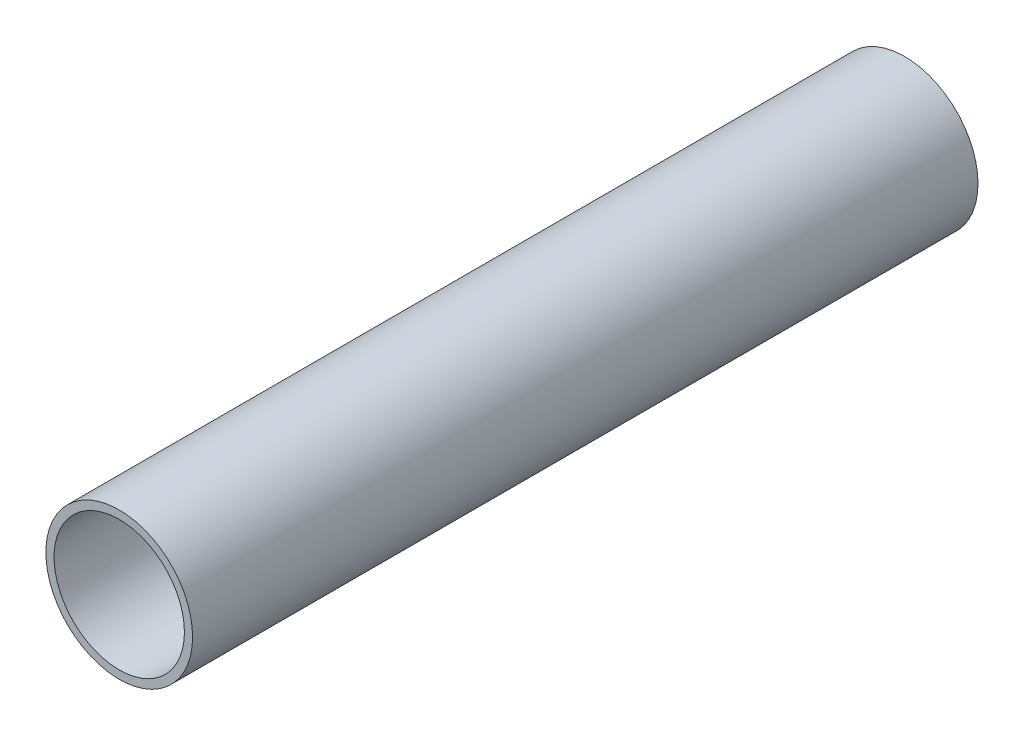
SolidWorks part; units mm, degrees
ref_plane "Front Plane" through (0, 0, 0) normal (0, 0, 1) x (1, 0, 0)
ref_plane "Top Plane" through (0, 0, 0) normal (0, 1, 0) x (1, 0, 0)
ref_plane "Right Plane" through (0, 0, 0) normal (1, 0, 0) x (0, 0, -1)
sketch "Sketch1" plane through (0, 0, 0) normal (0, 0, 1) x (1, 0, 0)
  circle A0 centre (0, 0) radius 50.595
  circle A1 centre (0, 0) radius 56.945
  dimension "D1" = 101.19
  dimension "D2" = 6.35
extrude "Boss-Extrude1" add sketch "Sketch1" along normal blind 609.6
